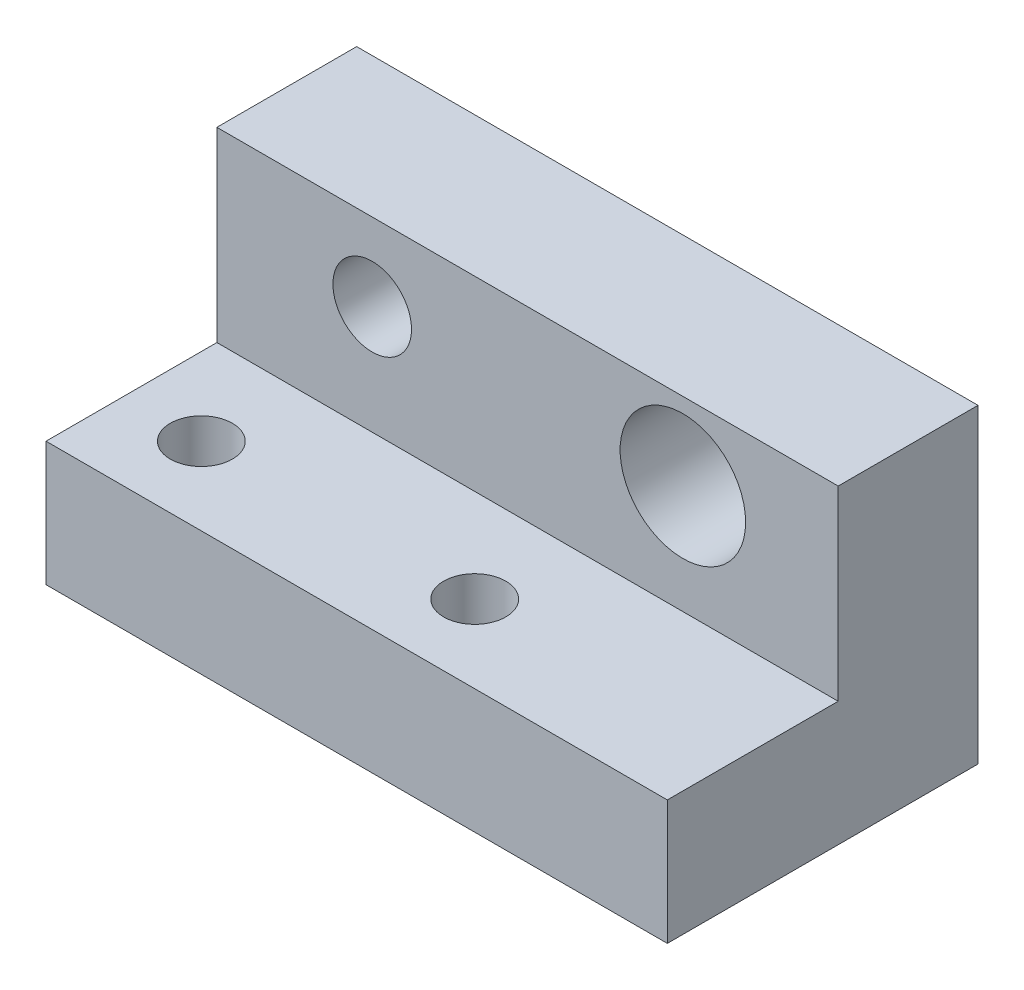
SolidWorks part; units mm, degrees
material "Delrin 2700 NC010, Low Viscosity Acetal Copolymer (SS)"
ref_plane "Front Plane" through (0, 0, 0) normal (0, 0, 1) x (1, 0, 0)
ref_plane "Top Plane" through (0, 0, 0) normal (0, 1, 0) x (1, 0, 0)
ref_plane "Right Plane" through (0, 0, 0) normal (1, 0, 0) x (0, 0, -1)
sketch "Sketch3" plane through (0, 0, 0) normal (1, 0, 0) x (0, 0, -1)
  line L0 (0, 0) -> (25.4, 0)
  line L1 (25.4, 0) -> (25.4, 25.4)
  line L2 (25.4, 25.4) -> (13.97, 25.4)
  line L3 (13.97, 25.4) -> (13.97, 10.16)
  line L4 (13.97, 10.16) -> (0, 10.16)
  line L5 (0, 10.16) -> (0, 0)
  dimension "D1" = 10.16
  dimension "D2" = 25.4
  dimension "D3" = 25.4
  dimension "D4" = 11.43
extrude "Boss-Extrude1" add sketch "Sketch3" against normal blind 50.8
sketch "Sketch4" plane through (0, 10.16, 0) normal (0, 1, 0) x (1, 0, 0)
  line L0 (-50.8, 25.4) -> (0, 25.4) construction
  line L1 (-50.8, 13.97) -> (-50.8, 0) construction
  line L2 (-50.8, 25.4) -> (-50.8, 13.97) construction
  circle A0 centre (-44.45, 6.35) radius 2.54
  circle A1 centre (-22.098, 6.35) radius 2.54
  dimension "D1" = 5.08
  dimension "D2" = 19.05
  dimension "D3" = 6.35
  dimension "D4" = 28.702
extrude "Cut-Extrude1" cut sketch "Sketch4" against normal through all
sketch "Sketch5" plane through (0, 0, -13.97) normal (0, 0, 1) x (1, 0, 0)
  line L0 (-50.8, 25.4) -> (-50.8, 10.16) construction
  line L1 (-50.8, 0) -> (0, 0) construction
  circle A0 centre (-38.1, 19.05) radius 3.2131
  circle A1 centre (-12.7, 19.05) radius 5.1308
  dimension "D1" = 6.4262
  dimension "D5" = 10.2616
  dimension "D2" = 12.7
  dimension "D3" = 19.05
  dimension "D4" = 38.1
extrude "Cut-Extrude2" cut sketch "Sketch5" against normal blind 50.8
